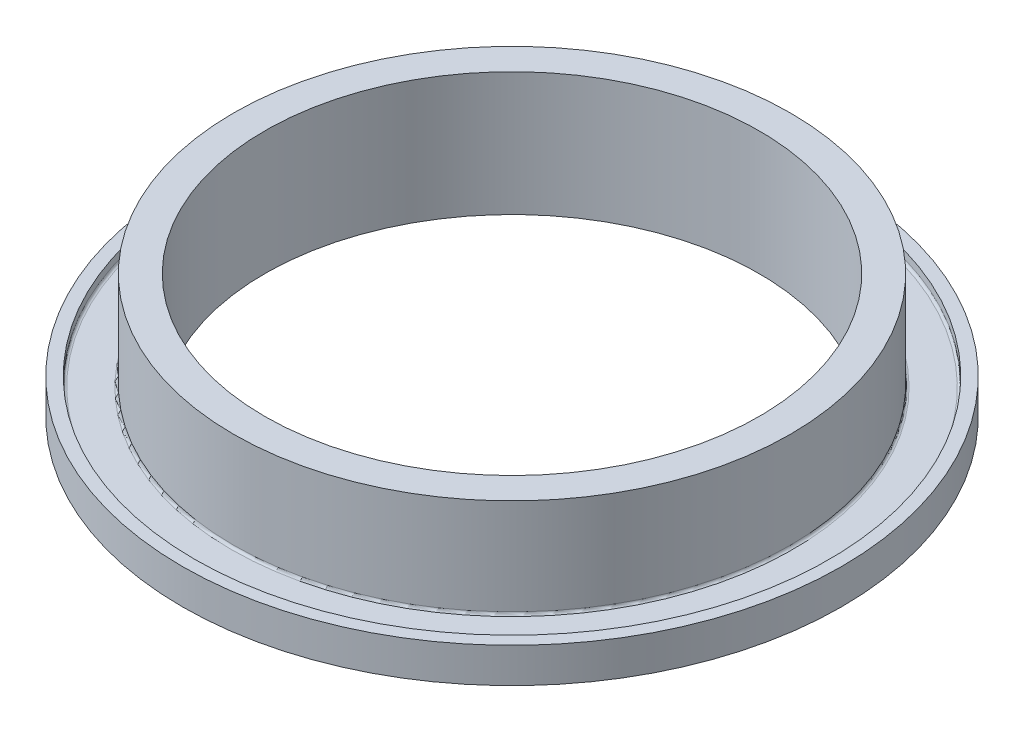
SolidWorks part; units mm, degrees
material "PVC Rigid"
ref_plane "Front Plane" through (0, 0, 0) normal (0, 0, 1) x (1, 0, 0)
ref_plane "Top Plane" through (0, 0, 0) normal (0, 1, 0) x (1, 0, 0)
ref_plane "Right Plane" through (0, 0, 0) normal (1, 0, 0) x (0, 0, -1)
sketch "Sketch1" plane through (0, 0, 0) normal (0, 1, 0) x (1, 0, 0)
  circle A0 centre (0, 0) radius 57.15
  circle A1 centre (0, 0) radius 50.7746
  dimension "D1" = 114.3
  dimension "D2" = 101.5492
extrude "Boss-Extrude1" add sketch "Sketch1" along normal blind 25.4
ref_axis "Axis1" through (0, 25.4, 0) along (0, -1, 0)
sketch "Sketch2" plane through (0, 0, 0) normal (0, 0, 1) x (1, 0, 0)
  line L0 (-57.15, 25.4) -> (-57.15, 0) construction
  line L1 (-57.15, 5.175) -> (-65.15, 5.175)
  line L2 (-57.15, 5.175) -> (-57.15, 2)
  line L3 (-57.15, 2) -> (-65.15, 2)
  line L4 (-57.15, 0) -> (57.15, 0) construction
  line L5 (-65.15, 5.175) -> (-65.15, 7.175)
  line L6 (-65.15, 0) -> (-67.69, 0)
  line L7 (-65.15, 0) -> (-65.15, 2)
  line L8 (-65.15, 7.175) -> (-67.69, 7.175)
  line L9 (-67.69, 0) -> (-67.69, 7.175)
  dimension "D1" = 8
  dimension "D2" = 2
  dimension "D3" = 3.175
  dimension "D4" = 2.54
revolve "Revolve1" add sketch "Sketch2" angle 360 about axis through (0, 25.4, 0) along (0, -1, 0)
fillet "Fillet1" radius 0.5 4 edges at (0, 5.175, 65.15) (0, 5.175, 57.15) (0, 2, 57.15) (0, 2, 65.15)
